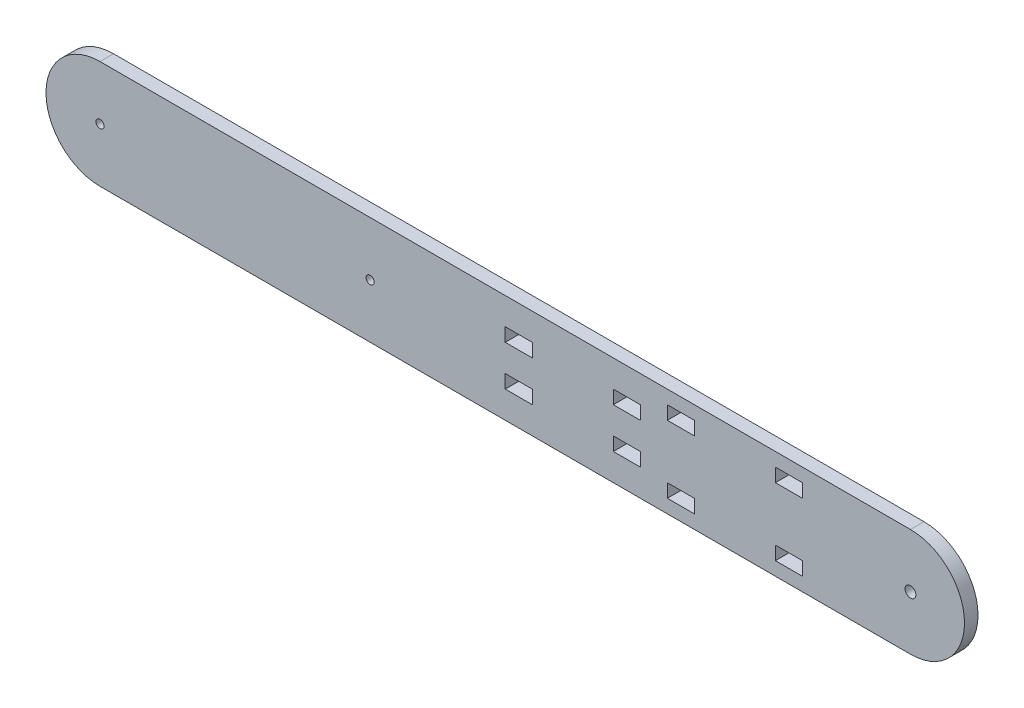
SolidWorks part; units mm, degrees
ref_plane "Front Plane" through (0, 0, 0) normal (0, 0, 1) x (1, 0, 0)
ref_plane "Top Plane" through (0, 0, 0) normal (0, 1, 0) x (1, 0, 0)
ref_plane "Right Plane" through (0, 0, 0) normal (1, 0, 0) x (0, 0, -1)
sketch "Sketch1" plane through (0, 0, 0) normal (0, 0, 1) x (1, 0, 0)
  line L0 (-126.9044, 0) -> (173.0956, 0) construction
  line L1 (-126.9044, 20) -> (173.0956, 20)
  line L2 (-126.9044, -20) -> (173.0956, -20)
  line L3 (173.0956, 15) -> (-126.9044, 15) construction
  line L4 (173.0956, 10) -> (-126.9044, 10) construction
  line L5 (-126.9044, -15) -> (173.0956, -15) construction
  line L6 (173.0956, -10) -> (-126.9044, -10) construction
  line L7 (-126.9044, -5) -> (173.0956, -5) construction
  line L8 (173.0956, 5) -> (-126.9044, 5) construction
  line L9 (23.0956, -20) -> (23.0956, 20) construction
  line L10 (-57.7377, 20) -> (-57.7377, -20) construction
  line L44 (23.0956, 10) -> (33.0956, 10)
  line L45 (23.0956, 10) -> (23.0956, 5)
  line L46 (23.0956, 5) -> (33.0956, 5)
  line L47 (33.0956, 10) -> (33.0956, 5)
  line L48 (23.0956, -5) -> (33.0956, -5)
  line L49 (23.0956, -5) -> (23.0956, -10)
  line L50 (23.0956, -10) -> (33.0956, -10)
  line L51 (33.0956, -5) -> (33.0956, -10)
  line L52 (63.0956, 10) -> (73.0956, 10)
  line L53 (63.0956, 10) -> (63.0956, 5)
  line L54 (63.0956, 5) -> (73.0956, 5)
  line L55 (73.0956, 10) -> (73.0956, 5)
  line L56 (63.0956, -5) -> (73.0956, -5)
  line L57 (63.0956, -5) -> (63.0956, -10)
  line L58 (63.0956, -10) -> (73.0956, -10)
  line L59 (73.0956, -5) -> (73.0956, -10)
  line L64 (123.0956, -10) -> (133.0956, -10)
  line L65 (123.0956, -10) -> (123.0956, -15)
  line L66 (123.0956, -15) -> (133.0956, -15)
  line L67 (133.0956, -10) -> (133.0956, -15)
  line L68 (123.0956, 15) -> (133.0956, 15)
  line L69 (123.0956, 15) -> (123.0956, 10)
  line L70 (123.0956, 10) -> (133.0956, 10)
  line L71 (133.0956, 15) -> (133.0956, 10)
  line L72 (83.0956, -10) -> (93.0956, -10)
  line L73 (83.0956, -10) -> (83.0956, -15)
  line L74 (83.0956, -15) -> (93.0956, -15)
  line L75 (93.0956, -10) -> (93.0956, -15)
  line L76 (83.0956, 10) -> (93.0956, 10)
  line L77 (83.0956, 10) -> (83.0956, 15)
  line L78 (83.0956, 15) -> (93.0956, 15)
  line L79 (93.0956, 10) -> (93.0956, 15)
  arc A0 (-126.9044, 20) -> (-126.9044, -20) centre (-126.9044, 0) ccw
  arc A1 (173.0956, -20) -> (173.0956, 20) centre (173.0956, 0) ccw
  circle A2 centre (-126.9044, 0) radius 1.5
  circle A3 centre (173.0956, 0) radius 2
  circle A5 centre (-26.9044, 0) radius 1.5
  point P3 (23.0956, 0)
  dimension "D3" = 3
  dimension "D4" = 4
  dimension "D22" = 3
  dimension "D23" = 100
  dimension "D1" = 300
  dimension "D2" = 40
  dimension "D5" = 5
  dimension "D6" = 5
  dimension "D7" = 5
  dimension "D8" = 10
  dimension "D9" = 5
  dimension "D10" = 5
  dimension "D11" = 150
extrude "Boss-Extrude1" add sketch "Sketch1" along normal blind 5
